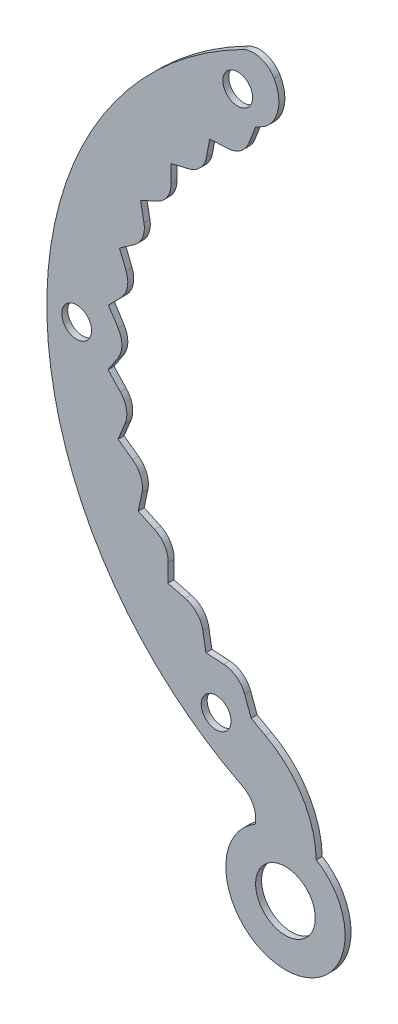
SolidWorks part; units mm, degrees
material "3003 Alaşım"
ref_plane "Ön Düzlem" through (0, 0, 0) normal (0, 0, 1) x (1, 0, 0)
ref_plane "Üst Düzlem" through (0, 0, 0) normal (0, 1, 0) x (1, 0, 0)
ref_plane "Sağ Düzlem" through (0, 0, 0) normal (1, 0, 0) x (0, 0, -1)
sketch "Çizim1" plane through (0, 0, 0) normal (0, 0, 1) x (1, 0, 0)
  line L0 (-50, 0) -> (-25, 0) construction
  line L1 (-25, 74.7114) -> (-25, -57.8833) construction
  line L3 (-25, 43.3013) -> (-26.1465, 40.3921)
  line L10 (-32.6937, 37.73) -> (-33.2521, 34.7773)
  line L11 (-32.6937, 37.73) -> (-29.6915, 37.8626)
  line L12 (-39.1845, 30.9355) -> (-36.2603, 31.6283)
  line L13 (-39.1845, 30.9355) -> (-39.1797, 27.9304)
  line L14 (-44.2872, 23.0451) -> (-41.5446, 24.2736)
  line L15 (-44.2872, 23.0451) -> (-43.7194, 20.0942)
  line L16 (-47.8209, 14.3384) -> (-45.3571, 16.059)
  line L17 (-47.8209, 14.3384) -> (-46.7103, 11.546)
  line L18 (-49.6606, 5.1236) -> (-47.5629, 7.2754)
  line L19 (-49.6606, 5.1236) -> (-48.0464, 2.5889)
  line L20 (-49.7411, -4.2726) -> (-48.0837, -1.7658)
  line L21 (-49.7411, -4.2726) -> (-47.6805, -6.46)
  line L22 (-48.0594, -13.5175) -> (-46.9011, -10.7445)
  line L23 (-48.0594, -13.5175) -> (-45.6255, -15.28)
  line L24 (-44.6753, -22.2835) -> (-44.057, -19.3426)
  line L25 (-44.6753, -22.2835) -> (-41.9541, -23.5587)
  line L26 (-39.7084, -30.2601) -> (-39.6522, -27.2555)
  line L27 (-39.7084, -30.2601) -> (-36.7965, -31.0028)
  line L28 (-33.3349, -37.1647) -> (-33.8427, -34.2028)
  line L29 (-33.3349, -37.1647) -> (-30.3354, -37.3487)
  line L30 (-25.7378, -42.8669) -> (-26.8343, -39.9385)
  line L31 (-25, -57.0526) -> (-25, -57.8833)
  line L33 (-15, -47.697) -> (-15, -66.5436) construction
  line L34 (-25, -66.5436) -> (-15, -66.5436) construction
  line L35 (-25, -54.5436) -> (-25, -66.5436) construction
  arc A0 (-27.1796, 53.4909) -> (-27.1875, -53.4868) centre (0, 0) ccw
  arc A3 (-23.4461, 44.162) -> (-21.9062, 51.9296) centre (-27.0983, 48.9224) ccw
  arc A4 (-26.1465, 40.3921) -> (-29.6915, 37.8626) centre (-29.8679, 41.8587) cw
  arc A5 (-33.2521, 34.7773) -> (-36.2603, 31.6283) centre (-37.1824, 35.5206) cw
  arc A6 (-39.1797, 27.9304) -> (-41.5446, 24.2736) centre (-43.1797, 27.9241) cw
  arc A7 (-43.7194, 20.0942) -> (-45.3571, 16.059) centre (-47.6474, 19.3384) cw
  arc A8 (-46.7103, 11.546) -> (-47.5629, 7.2754) centre (-50.4271, 10.0677) cw
  arc A9 (-48.0464, 2.5889) -> (-48.0837, -1.7658) centre (-51.4203, 0.4403) cw
  arc A10 (-47.6805, -6.46) -> (-46.9011, -10.7445) centre (-50.592, -9.2028) cw
  arc A11 (-45.6255, -15.28) -> (-44.057, -19.3426) centre (-47.9715, -18.5198) cw
  arc A12 (-41.9541, -23.5587) -> (-39.6522, -27.2555) centre (-43.6515, -27.1807) cw
  arc A13 (-36.7965, -31.0028) -> (-33.8427, -34.2028) centre (-37.7852, -34.8787) cw
  arc A14 (-30.3354, -37.3487) -> (-26.8343, -39.9385) centre (-30.5803, -41.3412) cw
  arc A15 (-23.4461, 44.162) -> (-25, 43.3013) centre (0, 0) ccw
  arc A16 (-20.8333, 45.453) -> (-15, -47.697) centre (0, 0) ccw construction
  arc A17 (-23.3522, -44.2117) -> (-14.8293, -57.9841) centre (-30.8249, -58.3594) cw
  arc A18 (-25, -57.8833) -> (-14.8293, -57.9841) centre (-20, -66.5436) ccw
  arc A19 (-25, 54.5436) -> (-25, -54.5436) centre (0, 0) ccw construction
  arc A20 (-27.1875, -53.4868) -> (-25, -57.0526) centre (-29, -57.0526) cw
  arc A21 (-27.1796, 53.4909) -> (-21.9062, 51.9296) centre (-25.3676, 49.9248) cw
  circle A22 centre (-20, -66.5436) radius 5
  arc A23 (-25.7378, -42.8669) -> (-23.3522, -44.2117) centre (0, 0) ccw
  circle A26 centre (-31.6201, -45.0019) radius 2.5
  circle A27 centre (-55, 0) radius 2.5
  circle A28 centre (-28.0006, 47.3388) radius 2.5
  point P9 (-25, 0)
  point P64 (-25, -54.5436)
  point P69 (0, 0)
  dimension "D1" = 60
  dimension "D2" = 10
  dimension "D4" = 4
  dimension "D6" = 16
  dimension "D7" = 4
  dimension "D8" = 4
  dimension "D9" = 10
  dimension "D3" = 25
  dimension "D5" = 11
extrude "Yükseklik-Ekstrüzyon2" add sketch "Çizim1" along normal blind 1
scale "Scale1" scale about centroid uniform scaling yes scale factor 0.5
